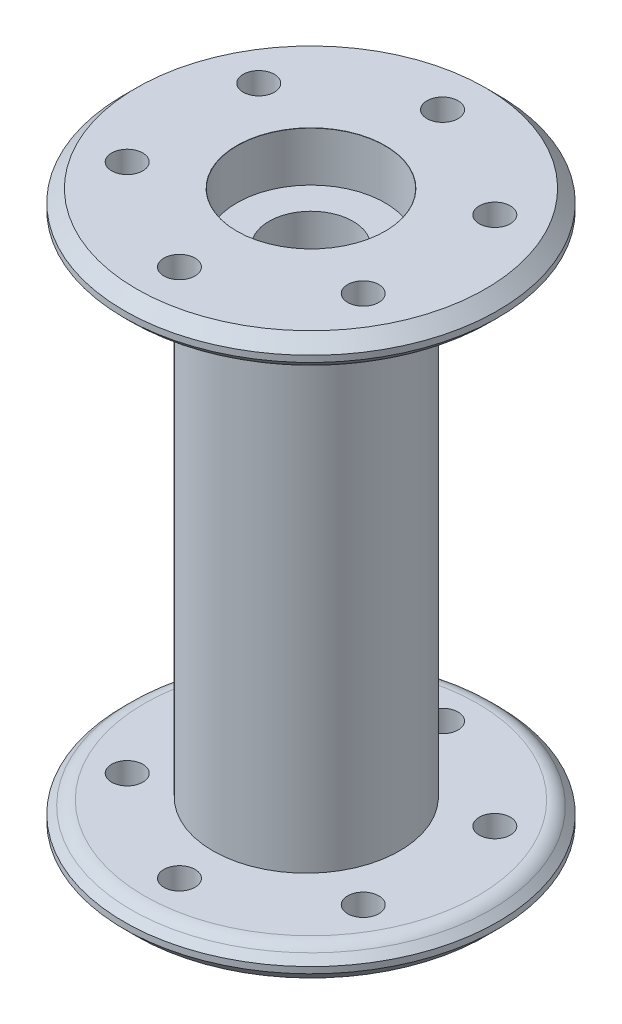
SolidWorks part; units mm, degrees
ref_plane "Front Plane" through (0, 0, 0) normal (0, 0, 1) x (1, 0, 0)
ref_plane "Top Plane" through (0, 0, 0) normal (0, 1, 0) x (1, 0, 0)
ref_plane "Right Plane" through (0, 0, 0) normal (1, 0, 0) x (0, 0, -1)
sketch "Sketch1" plane through (0, 0, 0) normal (0, 1, 0) x (1, 0, 0)
  circle A0 centre (-0.7578, 0) radius 15
  dimension "Shaft Diameter" = 30
extrude "Boss-Extrude1" add sketch "Sketch1" along normal mid plane 80
sketch "Sketch2" plane through (0, 40, 0) normal (0, 1, 0) x (1, 0, 0)
  circle A0 centre (0, 0) radius 30
  dimension "Cap Diameter" = 60
extrude "Boss-Extrude2" add sketch "Sketch2" along normal blind 5
chamfer "Chamfer1" distance 2 angle 45 2 edges at (0, 40, 30) (0, 45, 30)
sketch "Sketch3" plane through (0, 45, 0) normal (0, 1, 0) x (1, 0, 0)
  line L0 (0, 28) -> (-0.7578, 15) construction
  circle A0 centre (0, 0) radius 28 construction
  circle A1 centre (-0.7578, 0) radius 15 construction
  circle A2 centre (-0.3789, 21.5) radius 2.5
  dimension "D1" = 5
fillet "Fillet1" radius 3 1 edges at (0, 40, 28)
extrude "Cut-Extrude1" cut sketch "Sketch3" against normal through all
pattern_circular "CirPattern2" count 6 over 360 about axis through (0, 0, 0) along (0, 1, 0) of "Cut-Extrude1"
hole_wizard "CBORE for M12 Hex Head Bolt1" positions "Sketch4" profile "Sketch5" counterbore size "M12" standard "ANSI Metric" end condition through all
sketch "Sketch4" plane through (0, 45, 0) normal (0, 1, 0) x (1, 0, 0)
  point P0 (0, 0)
sketch "Sketch5" plane through (0, 45, 0) normal (1, 0, 0) x (0, 0, 1)
  line L0 (0, 0) -> (0, 90)
  line L1 (0, 90) -> (6.75, 90)
  line L3 (6.75, 90) -> (6.75, 7.95)
  line L4 (11.89, 7.95) -> (6.75, 7.95)
  line L5 (11.89, 7.95) -> (11.89, 0.025)
  line L6 (11.89, 0.025) -> (11.915, 0)
  line L7 (11.915, 0) -> (0, 0)
  line L8 (-11.89, 0.025) -> (-11.915, 0) construction
  line L11 (0, -6.35) -> (0, 107.95) construction
  dimension "Thru Hole Dia." = 13.5
  dimension "Thru Hole Depth" = 90
  dimension "C'Bore Dia." = 23.78
  dimension "C'Bore Depth" = 7.95
  dimension "Near C'Sink Dia." = 23.83
  dimension "Near C'Sink Angle" = 90
mirror "Mirror1" about plane through (0, 0, 0) normal (0, 1, 0) of "Cut-Extrude1", "Chamfer1", "CBORE for M12 Hex Head Bolt1", "CirPattern2", "Fillet1", "Boss-Extrude2"
